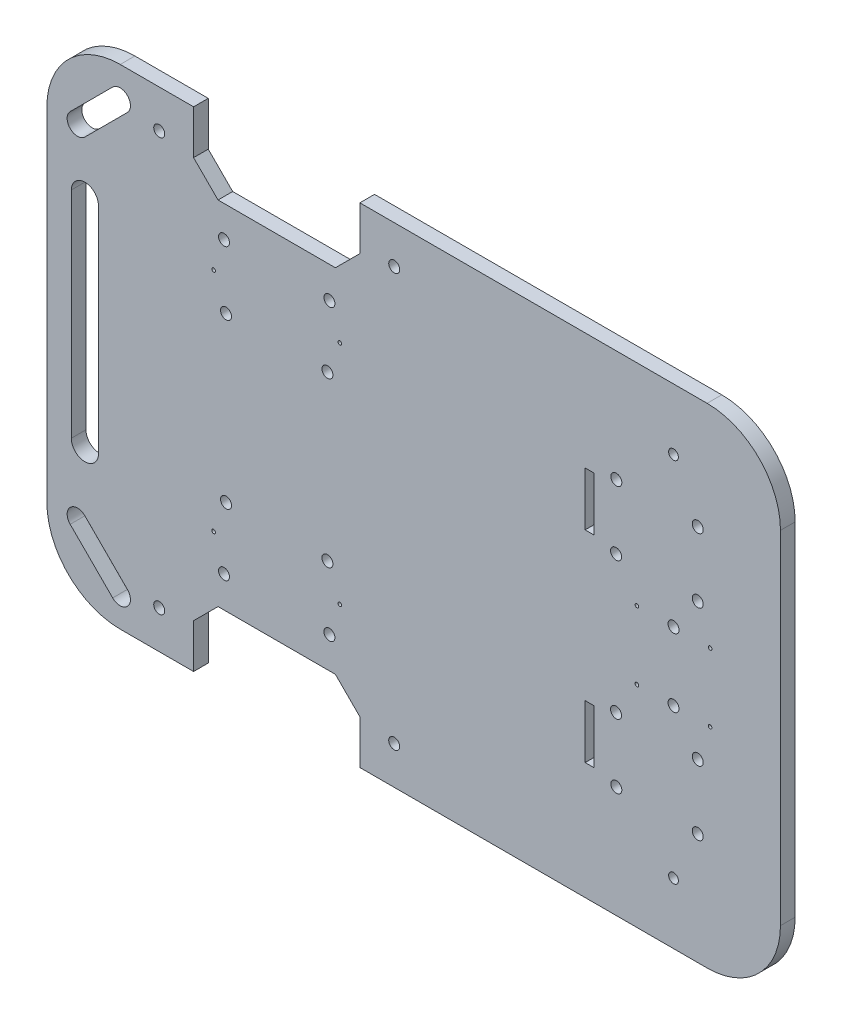
SolidWorks part; units mm, degrees
ref_plane "Front Plane" through (0, 0, 0) normal (0, 0, 1) x (1, 0, 0)
ref_plane "Top Plane" through (0, 0, 0) normal (0, 1, 0) x (1, 0, 0)
ref_plane "Right Plane" through (0, 0, 0) normal (1, 0, 0) x (0, 0, -1)
sketch "Sketch2" plane through (0, 0, 0) normal (0, 0, 1) x (1, 0, 0)
  line L0 (12.5417, 170.0761) -> (29.9239, 187.4583) construction
  line L1 (30, 0) -> (270, 0)
  line L2 (0, 30) -> (0, 170)
  line L3 (30, 200) -> (270, 200)
  line L4 (300, 30) -> (300, 170)
  line L14 (60, 0) -> (128, 0)
  line L20 (70, 28) -> (118, 28)
  line L21 (128, 0) -> (128, 18)
  line L26 (9.5365, 173.0813) -> (26.9187, 190.4635)
  line L27 (15.5469, 167.0708) -> (32.9292, 184.4531)
  line L28 (15.5469, 145.5395) -> (15.5469, 57.62) construction
  line L31 (12.5417, 29.9239) -> (29.9239, 12.5417) construction
  line L32 (9.5365, 26.9187) -> (26.9187, 9.5365)
  line L33 (15.5469, 32.9292) -> (32.9292, 15.5469)
  line L34 (21.0973, 145.5395) -> (21.0973, 57.62)
  line L35 (9.9965, 145.5395) -> (9.9965, 57.62)
  line L36 (300, 100) -> (0, 100) construction
  line L37 (150, 200) -> (150, 0) construction
  line L40 (300, 170) -> (184.9207, 170) construction
  line L43 (60, 200) -> (60, 0) construction
  line L48 (128, 0) -> (128, 200) construction
  line L51 (70, 172) -> (118, 172)
  line L52 (128, 200) -> (128, 182)
  line L53 (60, 200) -> (128, 200)
  line L54 (60, 200) -> (60, 182)
  line L57 (60, 0) -> (128, 0) construction
  line L58 (184.9207, 170) -> (184.9207, 30) construction
  line L59 (94, 0) -> (93, 100.25) construction
  line L60 (60, 200) -> (128, 200) construction
  line L61 (94, 200) -> (94, 145.5395) construction
  line L62 (60, 18) -> (60, 0)
  line L63 (300, 69.6075) -> (300, 30) construction
  line L64 (184.9207, 30) -> (300, 30) construction
  line L65 (300, 100) -> (300, 30) construction
  line L66 (184.9207, 100) -> (184.9207, 30) construction
  line L67 (242.4603, 170) -> (242.4603, 30) construction
  line L68 (214.7061, 100) -> (214.7061, 30) construction
  line L69 (270, 100) -> (270, 30) construction
  line L70 (118, 172) -> (128, 182)
  line L71 (60, 182) -> (70, 172)
  line L72 (214.7061, 100) -> (214.7061, 170) construction
  line L73 (60, 18) -> (70, 28)
  line L74 (118, 28) -> (128, 18)
  line L75 (270, 151.265) -> (270, 118.735) construction
  line L76 (214.7061, 65) -> (270.1406, 65.2225) construction
  line L77 (214.7061, 135) -> (270, 135) construction
  line L78 (270, 118.735) -> (214.7061, 118.735) construction
  line L79 (270, 151.265) -> (214.7061, 151.265) construction
  line L80 (270, 124.915) -> (214.7061, 124.915) construction
  line L81 (270, 145.085) -> (214.7061, 145.085) construction
  line L82 (222.3561, 151.265) -> (222.3561, 118.735) construction
  line L83 (262.5646, 151.265) -> (262.5646, 118.735) construction
  line L84 (214.7061, 145.085) -> (222.3561, 145.085) construction
  line L85 (214.7061, 147.44) -> (222.3561, 147.44) construction
  line L86 (252, 151.265) -> (252, 118.735) construction
  line L87 (241.4354, 151.265) -> (241.4354, 118.735) construction
  line L88 (234, 151.265) -> (234, 118.735) construction
  line L89 (256.2622, 86.035) -> (256.2622, 113.965) construction
  line L90 (256.2622, 111.715) -> (256.2622, 88.285) construction
  line L92 (300, 128) -> (168.2946, 128) construction
  line L93 (300, 121.825) -> (210.898, 121.825) construction
  line L94 (300, 124.915) -> (226.8243, 124.915) construction
  line L95 (270.6815, 151.265) -> (300, 151.265) construction
  line L96 (300, 151.265) -> (300, 148.175) construction
  line L97 (300, 148.175) -> (270.6815, 148.175) construction
  arc A4 (30, 200) -> (0, 170) centre (30, 170) ccw
  arc A5 (0, 30) -> (30, 0) centre (30, 30) ccw
  arc A6 (270, 0) -> (300, 30) centre (270, 30) ccw
  arc A7 (270, 200) -> (300, 170) centre (270, 170) cw
  arc A8 (9.5365, 173.0813) -> (15.5469, 167.0708) centre (12.5417, 170.0761) ccw
  arc A9 (32.9292, 184.4531) -> (26.9187, 190.4635) centre (29.9239, 187.4583) ccw
  arc A12 (9.5365, 26.9187) -> (15.5469, 32.9292) centre (12.5417, 29.9239) cw
  arc A13 (32.9292, 15.5469) -> (26.9187, 9.5365) centre (29.9239, 12.5417) cw
  arc A14 (21.0973, 145.5395) -> (9.9965, 145.5395) centre (15.5469, 145.5395) ccw
  arc A15 (9.9965, 57.62) -> (21.0973, 57.62) centre (15.5469, 57.62) ccw
  circle A23 centre (45.9517, 184.4531) radius 2.25
  circle A24 centre (45.9517, 15.5469) radius 2.25
  circle A26 centre (256.2622, 175) radius 2
  circle A119 centre (142.0483, 15.5469) radius 2.25
  circle A120 centre (142.0483, 184.4531) radius 2.25
  circle A122 centre (256.2622, 25) radius 2
  circle A139 centre (256.2622, 113.965) radius 2.25
  circle A140 centre (256.2622, 86.035) radius 2.25
  circle A145 centre (232.7714, 128.0778) radius 2.25
  circle A146 centre (266.1746, 128.005) radius 2.25
  circle A147 centre (266.1746, 154.355) radius 2.25
  circle A148 centre (232.8771, 154.4276) radius 2.25
  circle A149 centre (266.1746, 71.995) radius 2.25
  circle A150 centre (232.7714, 71.9222) radius 2.25
  circle A151 centre (232.8771, 45.5724) radius 2.25
  circle A152 centre (266.1746, 45.645) radius 2.25
  point P7 (0, 200)
  point P10 (0, 0)
  point P16 (300, 200)
  point P24 (60, 172)
  point P25 (128, 172)
  point P26 (21.2328, 178.7672)
  point P35 (21.2328, 21.2328)
  point P38 (32.9292, 190.4635)
  point P41 (15.5469, 101.5798)
  point P107 (256.2622, 100)
  point P118 (256.2622, 100)
  point P119 (256.2622, 100)
  point P121 (256.2622, 100)
  point P201 (128, 28)
  point P204 (60, 28)
  point P213 (60, 28)
  point P216 (128, 28)
  dimension "D3" = 30
  dimension "D4" = 30
  dimension "D5" = 27.93
  dimension "D6" = 30
  dimension "D12" = 28.8322
  dimension "D13" = 70
  dimension "D16" = 4.5
  dimension "D17" = 4.5
  dimension "D18" = 6.175
  dimension "D19" = 4
  dimension "D23" = 26.35
  dimension "D21" = 3.09
  dimension "D20" = 10
  dimension "D26" = 45
  dimension "D27" = 10
  dimension "D28" = 45
  dimension "D29" = 26.35
  dimension "D30" = 3.825
  dimension "D24" = 7.65
  dimension "D7" = 25
  dimension "D32" = 55.2939
  dimension "D46" = 4.5
  dimension "D15" = 28
  dimension "D1" = 300
  dimension "D2" = 200
  dimension "D8" = 68
  dimension "D9" = 28
  dimension "D10" = 8.5
  dimension "D14" = 28
  dimension "D22" = 68
extrude "Boss-Extrude2" add sketch "Sketch2" along normal blind 6
sketch "Sketch5" plane through (0, 0, 6) normal (0, 0, 1) x (1, 0, 0)
  line L0 (69.45, 53.7) -> (69.45, 33.1816) construction
  line L1 (112.55, 28) -> (112.55, 53.7) construction
  line L2 (118.55, 53.7) -> (118.55, 33.1816) construction
  line L3 (70, 28) -> (118, 28) construction
  line L4 (70, 172) -> (118, 172) construction
  line L5 (94, 28) -> (94, 172) construction
  line L6 (112.55, 28) -> (112.55, 53.7) construction
  line L7 (0, 100) -> (300, 100) construction
  line L8 (0, 30) -> (0, 170) construction
  line L9 (300, 30) -> (300, 170) construction
  line L10 (0, 53.7) -> (300, 53.7) construction
  line L11 (75.45, 28) -> (75.45, 53.7) construction
  circle A14 centre (73.27, 66.55) radius 2.25
  circle A15 centre (72.45, 40.85) radius 2.25
  circle A16 centre (115.55, 40.85) radius 2.25
  circle A17 centre (114.73, 66.55) radius 2.25
  circle A22 centre (115.55, 159.15) radius 2.25
  circle A23 centre (72.45, 159.15) radius 2.25
  circle A24 centre (73.27, 133.45) radius 2.25
  circle A25 centre (114.73, 133.45) radius 2.25
  dimension "D4" = 4.5
  dimension "D5" = 3
  dimension "D7" = 12.85
extrude "Cut-Extrude2" cut sketch "Sketch5" against normal through all
sketch "Sketch6" plane through (0, 0, 6) normal (0, 0, 1) x (1, 0, 0)
  line L0 (72.45, 156.9) -> (72.45, 146.3) construction
  line L1 (72.45, 146.3) -> (68.18, 146.3) construction
  line L2 (74.7, 159.15) -> (113.3, 159.15) construction
  line L3 (113.3, 159.15) -> (94, 159.15) construction
  line L4 (94, 159.15) -> (94, 135.6311) construction
  line L5 (0, 100) -> (78.0267, 100) construction
  line L6 (0, 30) -> (0, 170) construction
  line L7 (232.8771, 154.4276) -> (232.7714, 128.0778) construction
  line L8 (232.7714, 128.0778) -> (232.8242, 141.2527) construction
  line L9 (232.8242, 141.2527) -> (198.6985, 141.2527) construction
  line L10 (232.8771, 152.1776) -> (232.78, 130.2299) construction
  line L11 (223.6931, 69.7701) -> (220.1224, 69.7701)
  line L12 (223.6931, 152.1776) -> (220.1224, 152.1776)
  line L13 (223.6931, 152.1776) -> (223.6931, 130.2299)
  line L14 (223.6931, 130.2299) -> (220.1224, 130.2299)
  line L15 (220.1224, 152.1776) -> (220.1224, 130.2299)
  line L16 (220.1224, 47.8224) -> (220.1224, 69.7701)
  line L17 (223.6931, 47.8224) -> (220.1224, 47.8224)
  line L18 (223.6931, 47.8224) -> (223.6931, 69.7701)
  circle A0 centre (72.45, 159.15) radius 2.25 construction
  circle A1 centre (68.18, 146.3) radius 0.75
  circle A2 centre (115.55, 159.15) radius 2.25 construction
  circle A3 centre (119.82, 146.3) radius 0.75
  circle A4 centre (119.82, 53.7) radius 0.75
  circle A5 centre (68.18, 53.7) radius 0.75
  circle A6 centre (232.8771, 154.4276) radius 2.25 construction
extrude "Cut-Extrude3" cut sketch "Sketch6" against normal through all
sketch "Sketch7" plane through (0, 0, 6) normal (0, 0, 1) x (1, 0, 0)
  line L0 (256.2622, 113.965) -> (241.2922, 113.965) construction
  line L1 (256.2622, 113.965) -> (256.2622, 86.035) construction
  line L2 (256.2622, 86.035) -> (256.2622, 100) construction
  line L3 (256.2622, 100) -> (248.3366, 100) construction
  circle A0 centre (241.2922, 113.965) radius 0.75
  circle A1 centre (241.2922, 86.035) radius 0.75
  circle A2 centre (271.2322, 86.035) radius 0.75
  circle A3 centre (271.2322, 113.965) radius 0.75
  dimension "D1" = 14.97
extrude "Cut-Extrude4" cut sketch "Sketch7" against normal through all
